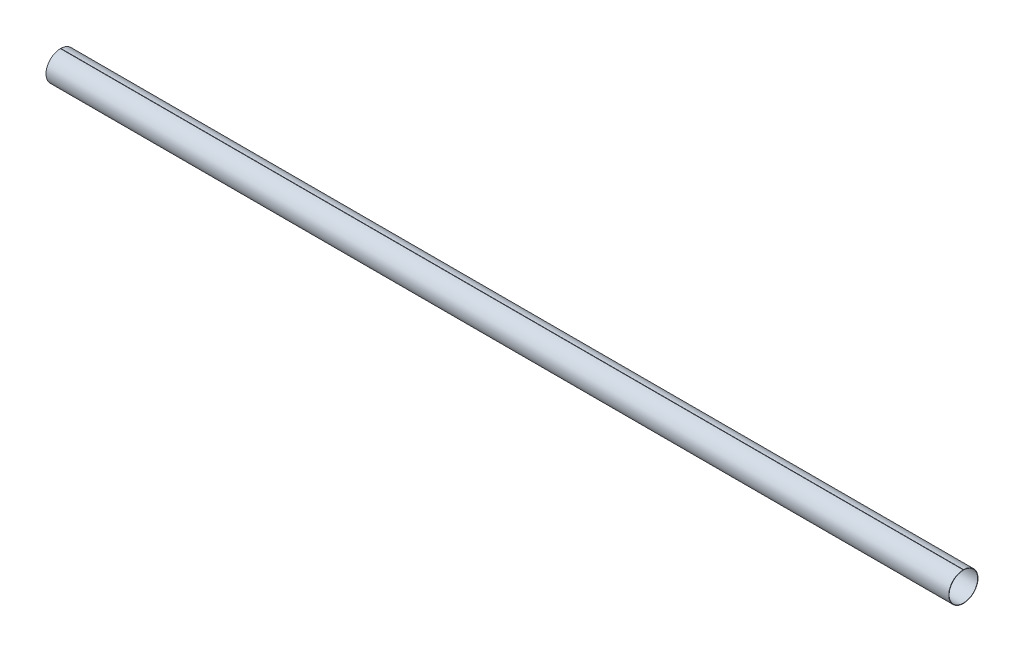
SolidWorks part; units mm, degrees
ref_plane "Front Plane" through (0, 0, 0) normal (0, 0, 1) x (1, 0, 0)
ref_plane "Top Plane" through (0, 0, 0) normal (0, 1, 0) x (1, 0, 0)
ref_plane "Right Plane" through (0, 0, 0) normal (1, 0, 0) x (0, 0, -1)
sketch "Sketch1" plane through (0, 0, 0) normal (1, 0, 0) x (0, 0, -1)
  line L0 (0, 0) -> (0, 54.5562) construction
  line L1 (-0.5, 40.4969) -> (-0.5, 39.4968)
  line L2 (0.5, 40.4969) -> (0.5, 39.4968)
  arc A0 (-0.5, 40.4969) -> (0.5, 40.4969) centre (0, 0) ccw
  arc A1 (-0.5, 39.4968) -> (0.5, 39.4968) centre (0, 0) ccw
  circle A3 centre (0, 0) radius 39.5 construction
  circle A4 centre (0, 0) radius 40.5 construction
  point P4 (38.4913, 11.768)
  point P9 (39.25, 0)
  dimension "D1" = 81
  dimension "D3" = 1
  dimension "D4" = 0.5
  dimension "D2" = 1
extrude "Boss-Extrude1" add sketch "Sketch1" along normal blind 2500
